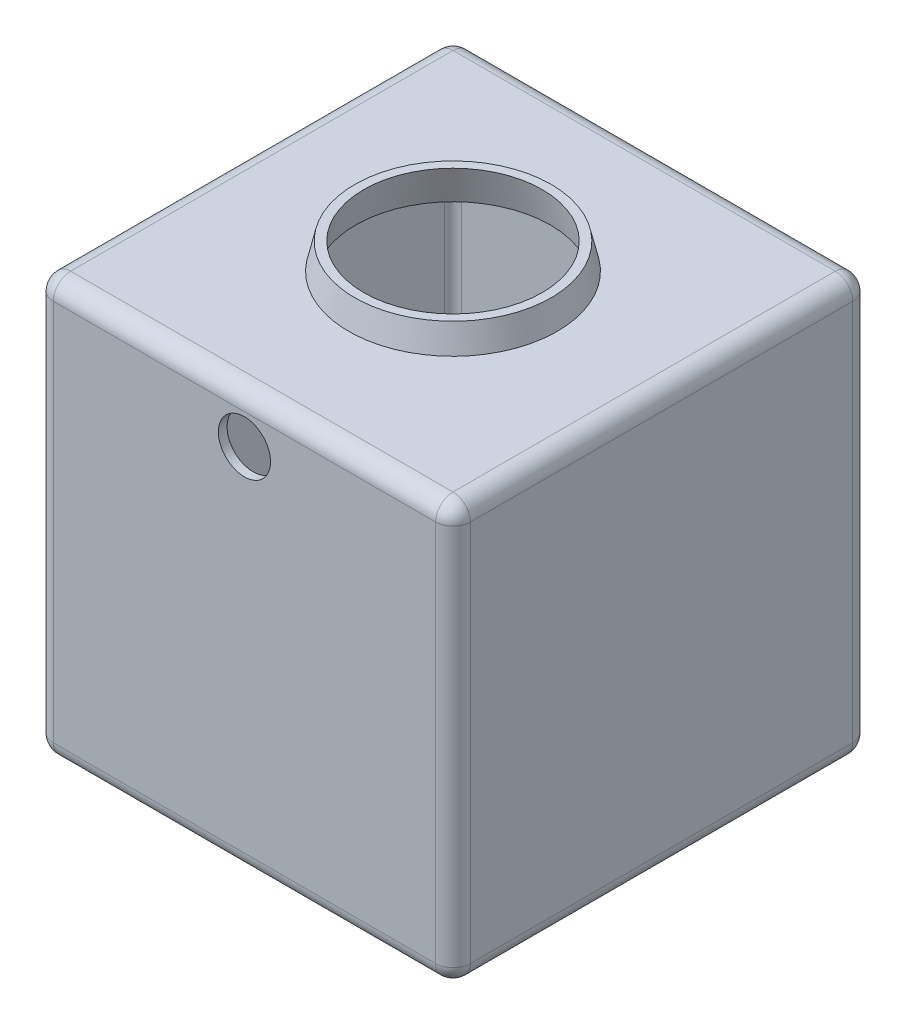
SolidWorks part; units mm, degrees
ref_plane "Front Plane" through (0, 0, 0) normal (0, 0, 1) x (1, 0, 0)
ref_plane "Top Plane" through (0, 0, 0) normal (0, 1, 0) x (1, 0, 0)
ref_plane "Right Plane" through (0, 0, 0) normal (1, 0, 0) x (0, 0, -1)
sketch "Sketch1" plane through (0, 0, 0) normal (0, 0, 1) x (1, 0, 0)
  line L1 (0, 0) -> (480, 0)
  line L2 (0, 0) -> (0, -480)
  line L3 (0, -480) -> (480, -480)
  line L4 (480, 0) -> (480, -480)
  dimension "D1" = 480
  dimension "D2" = 480
extrude "Boss-Extrude1" add sketch "Sketch1" along normal mid plane 480
fillet "Fillet1" radius 20 12 edges at (0, 0, 0) (0, -480, 0) (240, 0, 240) (240, -480, 240) (0, -240, 240) (240, -480, -240) (240, 0, -240) (0, -240, -240) (480, -480, 0) (480, -240, 240) (480, 0, 0) (480, -240, -240)
sketch "Sketch2" plane through (0, 0, 0) normal (0, 0, 1) x (1, 0, 0)
  line L0 (20, 0) -> (460, 0) construction
  line L1 (240, 0) -> (360, 0)
  line L2 (240, 0) -> (240, 30)
  line L3 (240, 30) -> (353, 30)
  line L5 (20, -240) -> (460, -240) construction
  line L12 (20, -20) -> (20, -460) construction
  line L13 (460, -460) -> (460, -20) construction
  line L18 (360, 0) -> (353, 30)
  line L19 (360, -480) -> (353, -510)
  line L20 (240, -510) -> (353, -510)
  line L21 (240, -480) -> (240, -510)
  line L22 (240, -480) -> (360, -480)
  dimension "D1" = 113
  dimension "D2" = 30
  dimension "D3" = 120
revolve "Revolve1" add sketch "Sketch2" angle 360 about L2
shell "Shell1" thickness 10
sketch "Sketch3" plane through (0, 0, 0) normal (0, 0, 1) x (1, 0, 0)
  line L0 (460, -20) -> (20, -20) construction
  circle A0 centre (240, -55) radius 30
  point P5 (240, -20)
  dimension "D1" = 60
  dimension "D2" = 35
extrude "Cut-Extrude1" cut sketch "Sketch3" against normal through all both and the other way through all
scale "Scale1" scale about origin uniform scaling yes scale factor 0.5
